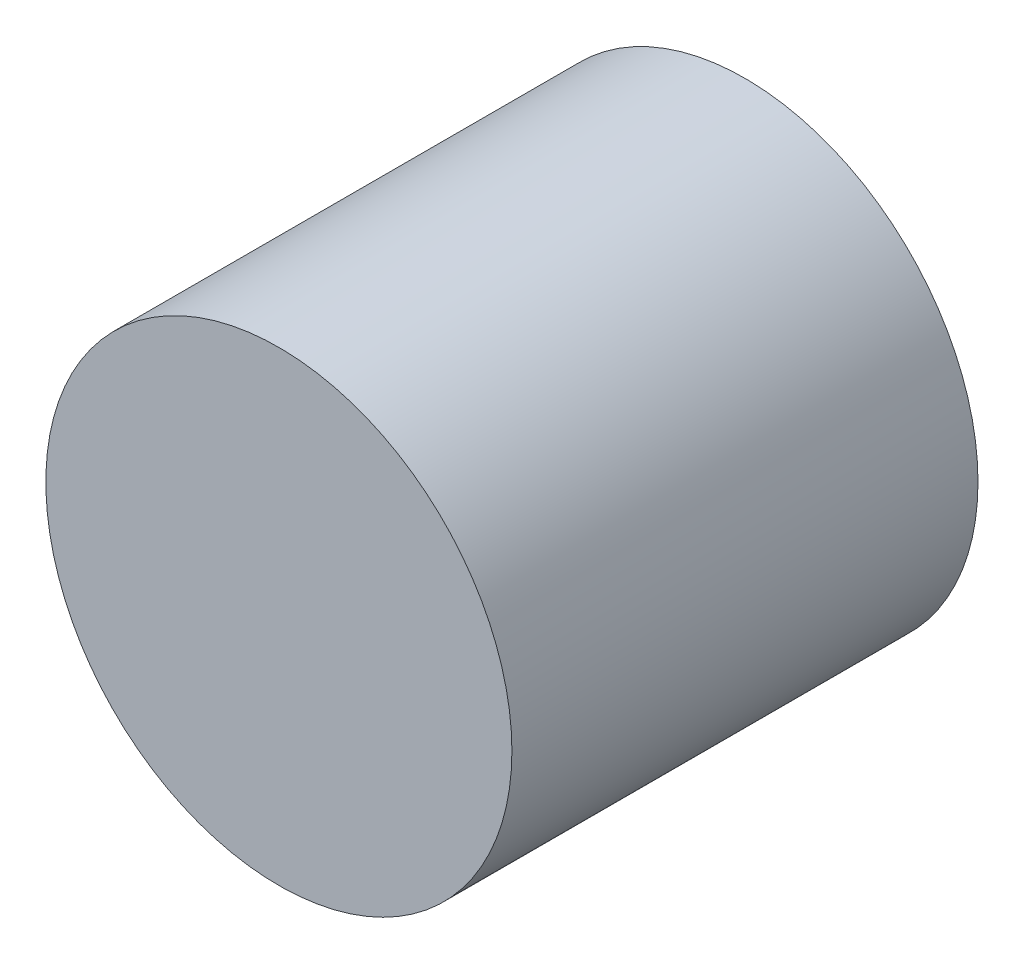
SolidWorks part; units mm, degrees
ref_plane "Front" through (0, 0, 0) normal (0, 0, 1) x (1, 0, 0)
ref_plane "Top" through (0, 0, 0) normal (0, 1, 0) x (1, 0, 0)
ref_plane "Right" through (0, 0, 0) normal (1, 0, 0) x (0, 0, -1)
sketch "Sketch1" plane through (0, 0, 0) normal (0, 0, 1) x (1, 0, 0)
  circle A0 centre (0, 0) radius 8.5
  dimension "D1" = 17
extrude "Boss-Extrude1" add sketch "Sketch1" along normal blind 17
